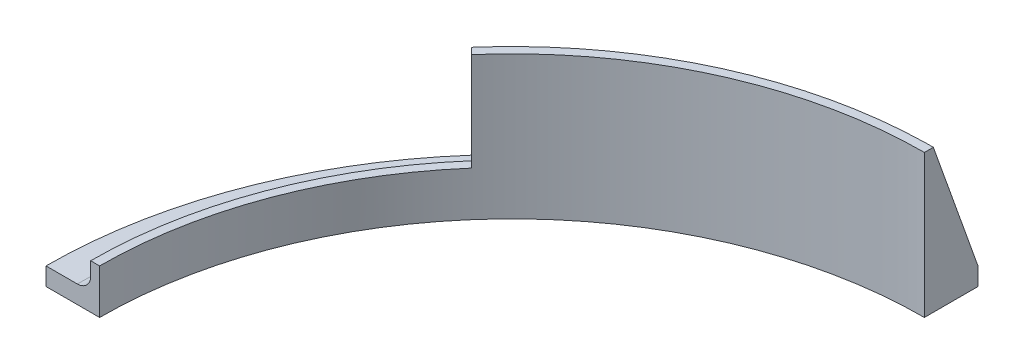
SolidWorks part; units mm, degrees
material "PET"
ref_plane "Front" through (0, 0, 0) normal (0, 0, 1) x (1, 0, 0)
ref_plane "Top" through (0, 0, 0) normal (0, 1, 0) x (1, 0, 0)
ref_plane "Right" through (0, 0, 0) normal (1, 0, 0) x (0, 0, -1)
sketch "Sketch1" plane through (0, 0, 0) normal (0, 1, 0) x (1, 0, 0)
  line L0 (0, 146.558) -> (0, 165.608)
  line L1 (-146.558, 0) -> (-165.608, 0)
  arc A0 (0, 146.558) -> (-146.558, 0) centre (0, 0) ccw
  arc A1 (0, 165.608) -> (-165.608, 0) centre (0, 0) ccw
  point P15 (0, 156.083)
  dimension "D2" = 146.558
  dimension "D1" = 19.05
extrude "Boss-Extrude1" add sketch "Sketch1" along normal blind 6.35 contours A0 L1 A1 L0
sketch "Sketch4" plane through (0, 6.35, 0) normal (0, 1, 0) x (1, 0, 0)
  line L2 (-149.733, 0) -> (-146.558, 0)
  line L3 (0, 146.558) -> (0, 149.733)
  line L4 (0, 146.558) -> (0, 165.608) construction
  arc A0 (-146.558, 0) -> (0, 146.558) centre (0, 0) cw
  arc A1 (0, 146.558) -> (-146.558, 0) centre (0, 0) ccw construction
  arc A2 (-149.733, 0) -> (0, 149.733) centre (0, 0) cw
  dimension "D1" = 3.175
extrude "Boss-Extrude2" add sketch "Sketch4" along normal blind 44.45
sketch "Sketch5" plane through (0, 50.8, 0) normal (0, 1, 0) x (1, 0, 0)
  line L0 (-105.8772, 105.8772) -> (-103.6322, 103.6322) construction
  line L1 (-146.558, 0) -> (-149.733, 0)
  line L2 (-112.8174, 98.449) -> (-110.567, 96.1986)
  arc A0 (0, 149.733) -> (-149.733, 0) centre (0, 0) ccw construction
  arc A1 (0, 146.558) -> (-146.558, 0) centre (0, 0) ccw construction
  arc A2 (-110.567, 96.1986) -> (-146.558, 0) centre (0, 0) ccw
  arc A3 (-112.8174, 98.449) -> (-149.733, 0) centre (0, 0) ccw
  dimension "D1" = 10.16
  dimension "D2" = 10.16
extrude "Cut-Extrude2" cut sketch "Sketch5" against normal offset from surface 9.525 and the other way through all up to face at (-95.1626, 6.35, -95.1626)
sketch "Sketch8" plane through (0, 6.35, 0) normal (0, 1, 0) x (1, 0, 0)
  line L0 (0, 149.733) -> (0, 165.608) construction
  line L1 (-143.383, 65.5843) -> (-87.8583, 130.9233) construction
  line L2 (-87.8583, 130.9233) -> (-6.35, 157.5426) construction
  circle A0 centre (0, 0) radius 157.6705 construction
  point P0 (-6.35, 157.5426)
  point P2 (-87.8583, 130.9233)
  point P4 (-143.383, 65.5843)
  point P14 (0, 157.6705)
  dimension "D1" = 6.35
  dimension "D2" = 85.7449
hole_wizard "#10-32 Tapped Hole1" positions "Sketch8" profile "Sketch7" tap size "#10-32" standard "ANSI Inch" end condition up to next
sketch "Sketch7" plane through (-6.35, 6.35, -157.5426) normal (1, 0, 0) x (0, 0, 1)
  line L0 (0, 0) -> (0, 6.35)
  line L1 (0, 6.35) -> (2.0193, 6.35)
  line L2 (2.0193, 6.35) -> (2.0193, 0)
  line L5 (2.0193, 0) -> (0, 0)
  line L11 (0, -6.35) -> (0, 107.95) construction
  dimension "Thru Tap Drill Dia." = 4.0386
  dimension "Thru Tap Drill Depth" = 6.35
cosmetic thread "Hole Thread1" parameters "D2"=4.826
cosmetic thread "Hole Thread2" parameters "D2"=4.826
cosmetic thread "Hole Thread3" parameters "D2"=4.826
sketch "Sketch9" plane through (0, 0, 0) normal (1, 0, 0) x (0, 0, -1)
  line L0 (149.733, 50.8) -> (165.608, 6.35)
  line L1 (149.733, 50.8) -> (146.558, 50.8)
  line L2 (146.558, 50.8) -> (146.558, 6.35)
  line L3 (146.558, 50.8) -> (146.558, 0) construction
  line L4 (146.558, 6.35) -> (165.608, 6.35)
extrude "Boss-Extrude5" add sketch "Sketch9" against normal blind 3.175
pattern_circular "CirPattern1" count 2 every 47.375 about axis through (0, 0, 0) along (0, 1, 0) of "Boss-Extrude5"
fillet "Fillet1" radius 4.7625 2 edges at (-61.6054, 6.35, -136.4725) (-140.0622, 6.35, -52.9391)
mirror "Mirror2" [suppressed] about plane through (0, 0, 0) normal (1, 0, 0)
cosmetic thread "Hole Thread4" [suppressed] parameters "D2"=4.826
cosmetic thread "Hole Thread5" [suppressed] parameters "D2"=4.826
cosmetic thread "Hole Thread6" [suppressed] parameters "D2"=4.826
delete or keep bodies "Body-Delete/Keep 1" [suppressed] type delete bodies bodies 118
